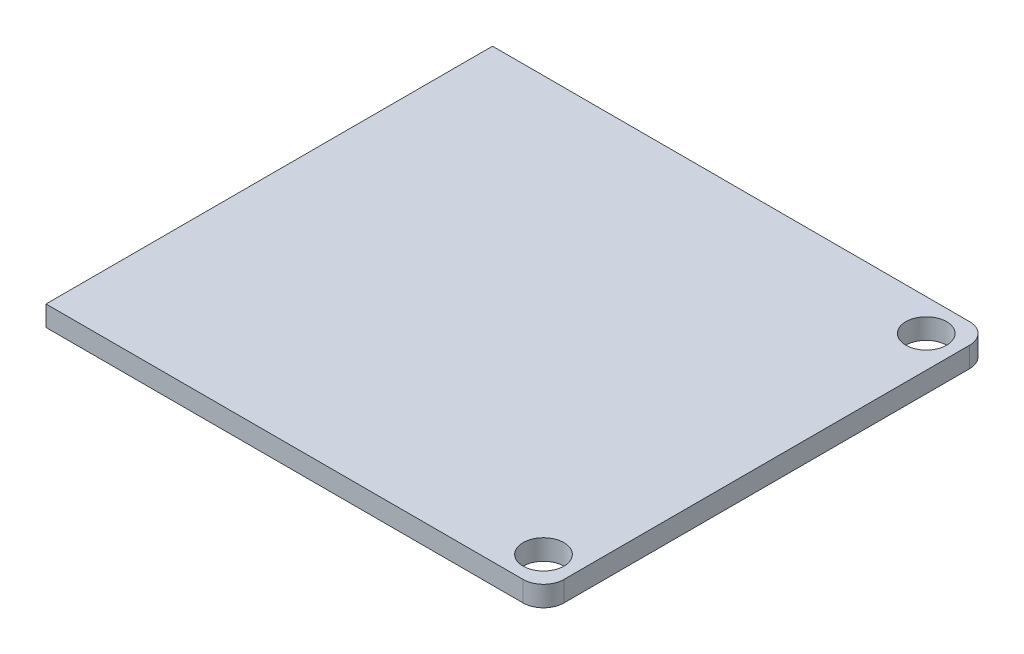
SolidWorks part; units mm, degrees
ref_plane "Спереди" through (0, 0, 0) normal (0, 0, 1) x (1, 0, 0)
ref_plane "Сверху" through (0, 0, 0) normal (0, 1, 0) x (1, 0, 0)
ref_plane "Справа" through (0, 0, 0) normal (1, 0, 0) x (0, 0, -1)
sketch "Sketch1" plane through (0, 0, 0) normal (0, 1, 0) x (1, 0, 0)
  line L1 (-19.5, -17.5) -> (19.5, -17.5)
  line L2 (-19.5, -17.5) -> (-19.5, 17.5)
  line L3 (-19.5, 17.5) -> (19.5, 17.5)
  line L4 (19.5, -17.5) -> (19.5, 17.5)
  line L5 (-19.5, -17.5) -> (19.5, 17.5) construction
  line L6 (-19.5, 17.5) -> (19.5, -17.5) construction
  point P0 (0, 0)
  dimension "D1" = 39
  dimension "D2" = 35
extrude "Boss-Extrude1" add sketch "Sketch1" along normal blind 1.6
sketch "Sketch2" plane through (0, 1.6, 0) normal (0, 1, 0) x (1, 0, 0)
  line L2 (19.5, -17.5) -> (19.5, 17.5) construction
  line L3 (19.5, 17.5) -> (-19.5, 17.5) construction
  line L4 (-19.5, -17.5) -> (19.5, -17.5) construction
  circle A0 centre (17, 15) radius 1.6
  circle A1 centre (17, -15) radius 1.6
  point P8 (0, 0)
  dimension "D1" = 3.2
  dimension "D2" = 2.5
  dimension "D3" = 2.5
  dimension "D4" = 2.5
extrude "Cut-Extrude1" cut sketch "Sketch2" against normal up to next
fillet "Fillet1" radius 1.6 2 edges at (19.5, 0.8, 17.5) (19.5, 0.8, -17.5)
